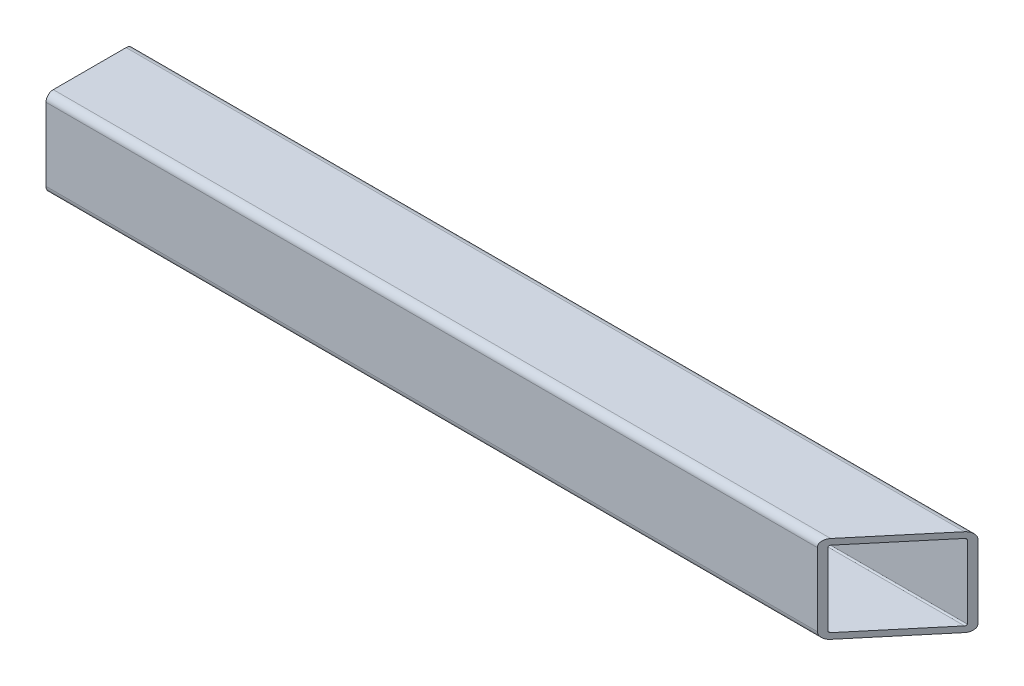
SolidWorks part; units mm, degrees
ref_plane "Front Plane" through (0, 0, 0) normal (0, 0, 1) x (1, 0, 0)
ref_plane "Top Plane" through (0, 0, 0) normal (0, 1, 0) x (1, 0, 0)
ref_plane "Right Plane" through (0, 0, 0) normal (1, 0, 0) x (0, 0, -1)
sketch "Sketch1" plane through (0, 0, 0) normal (1, 0, 0) x (0, 0, -1)
  line L1 (-15.875, 19.05) -> (15.875, 19.05)
  line L2 (-19.05, 15.875) -> (-19.05, -15.875)
  line L3 (-15.875, -19.05) -> (15.875, -19.05)
  line L4 (19.05, 15.875) -> (19.05, -15.875)
  line L5 (-19.05, 19.05) -> (19.05, -19.05) construction
  line L6 (-19.05, -19.05) -> (19.05, 19.05) construction
  arc A0 (-19.05, -15.875) -> (-15.875, -19.05) centre (-15.875, -15.875) ccw
  arc A1 (15.875, -19.05) -> (19.05, -15.875) centre (15.875, -15.875) ccw
  arc A2 (19.05, 15.875) -> (15.875, 19.05) centre (15.875, 15.875) ccw
  arc A3 (-15.875, 19.05) -> (-19.05, 15.875) centre (-15.875, 15.875) ccw
  point P0 (0, 0)
  dimension "D3" = 3.175
  dimension "D1" = 38.1
  dimension "D2" = 38.1
extrude "Extrude-Thin1" add sketch "Sketch1" along normal mid plane 368.3 thin
sketch "Sketch3" plane through (0, 19.05, 0) normal (0, 1, 0) x (1, 0, 0)
  line L0 (184.15, 15.875) -> (184.15, -15.875) construction
  line L1 (184.15, 19.05) -> (152.1803, -19.05)
  line L2 (184.15, -19.05) -> (-184.15, -19.05) construction
  dimension "D1" = 40
sketch "Sketch4" plane through (-184.15, 0, 0) normal (-1, 0, 0) x (0, 0, 1)
  line L0 (16.51, 0) -> (-16.51, 0) construction
  line L1 (16.51, 15.875) -> (16.51, -15.875) construction
  line L2 (-16.51, -15.875) -> (-16.51, 15.875) construction
  line L3 (0, 16.51) -> (0, -16.51) construction
  line L4 (-15.875, 16.51) -> (15.875, 16.51) construction
  line L5 (15.875, -16.51) -> (-15.875, -16.51) construction
extrude "Cut-Extrude1" cut sketch "Sketch3" against normal through all and the other way through all
